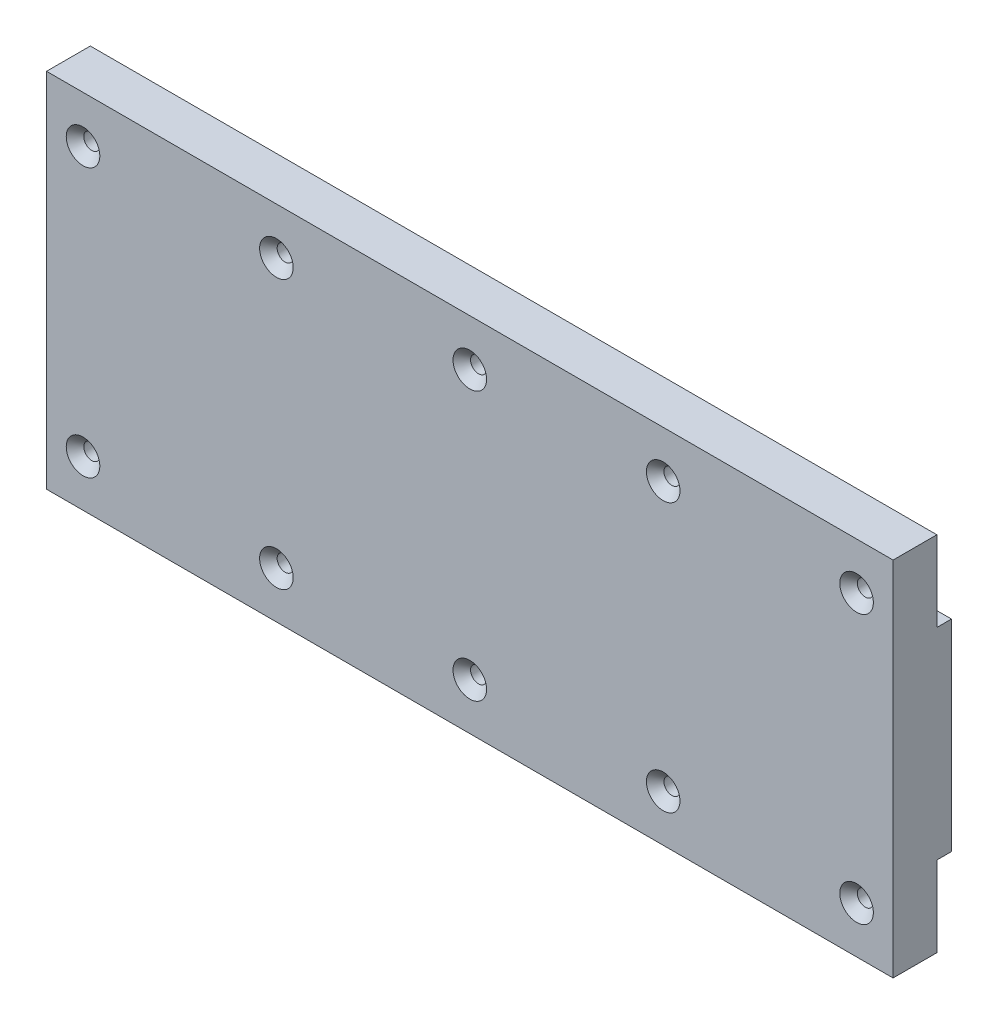
SolidWorks part; units mm, degrees
ref_plane "Alzado" through (0, 0, 0) normal (0, 0, 1) x (1, 0, 0)
ref_plane "Planta" through (0, 0, 0) normal (0, 1, 0) x (1, 0, 0)
ref_plane "Vista lateral" through (0, 0, 0) normal (1, 0, 0) x (0, 0, -1)
sketch "Croquis2" plane through (0, 0, 0) normal (1, 0, 0) x (0, 0, -1)
  line L0 (0, 0) -> (0, 248)
  line L1 (0, 248) -> (30, 248)
  line L2 (0, 0) -> (30, 0)
  line L4 (40, 193) -> (40, 55)
  line L5 (30, 248) -> (30, 193)
  line L6 (30, 193) -> (40, 193)
  line L7 (30, 0) -> (30, 55)
  line L8 (30, 55) -> (40, 55)
  point P10 (40, 124)
  dimension "D1" = 30
  dimension "D2" = 248
extrude "Saliente-Extruir1" add sketch "Croquis2" along normal blind 580
sketch "Croquis3" plane through (0, 0, 0) normal (0, 0, 1) x (1, 0, 0)
  line L0 (0, 124) -> (580, 124) construction
  line L1 (0, 248) -> (0, 0) construction
  line L2 (580, 248) -> (580, 0) construction
  line L3 (580, 0) -> (0, 0) construction
  line L4 (25, 216) -> (157.5, 216) construction
  circle A0 centre (25, 216) radius 5.5
  circle A1 centre (25, 32) radius 5.5
  circle A3 centre (157.5, 216) radius 5.5
  circle A4 centre (157.5, 32) radius 5.5
  circle A5 centre (290, 216) radius 5.5
  circle A6 centre (290, 32) radius 5.5
  circle A7 centre (422.5, 216) radius 5.5
  circle A8 centre (422.5, 32) radius 5.5
  circle A9 centre (555, 216) radius 5.5
  circle A10 centre (555, 32) radius 5.5
  dimension "D3" = 32
  dimension "D4" = 11
  dimension "D5" = 11
  dimension "D1" = 184
  dimension "D2" = 25
  dimension "D8" = 132.5
  dimension "D7" = 5
extrude "Cortar-Extruir1" cut sketch "Croquis3" against normal blind 580
chamfer "Chaflán2" distance 6 angle 45 10 edges at (560.5, 32, 0) (560.5, 216, 0) (428, 216, 0) (428, 32, 0) (295.5, 32, 0) (295.5, 216, 0) (163, 216, 0) (163, 32, 0) (30.5, 32, 0) (30.5, 216, 0)
